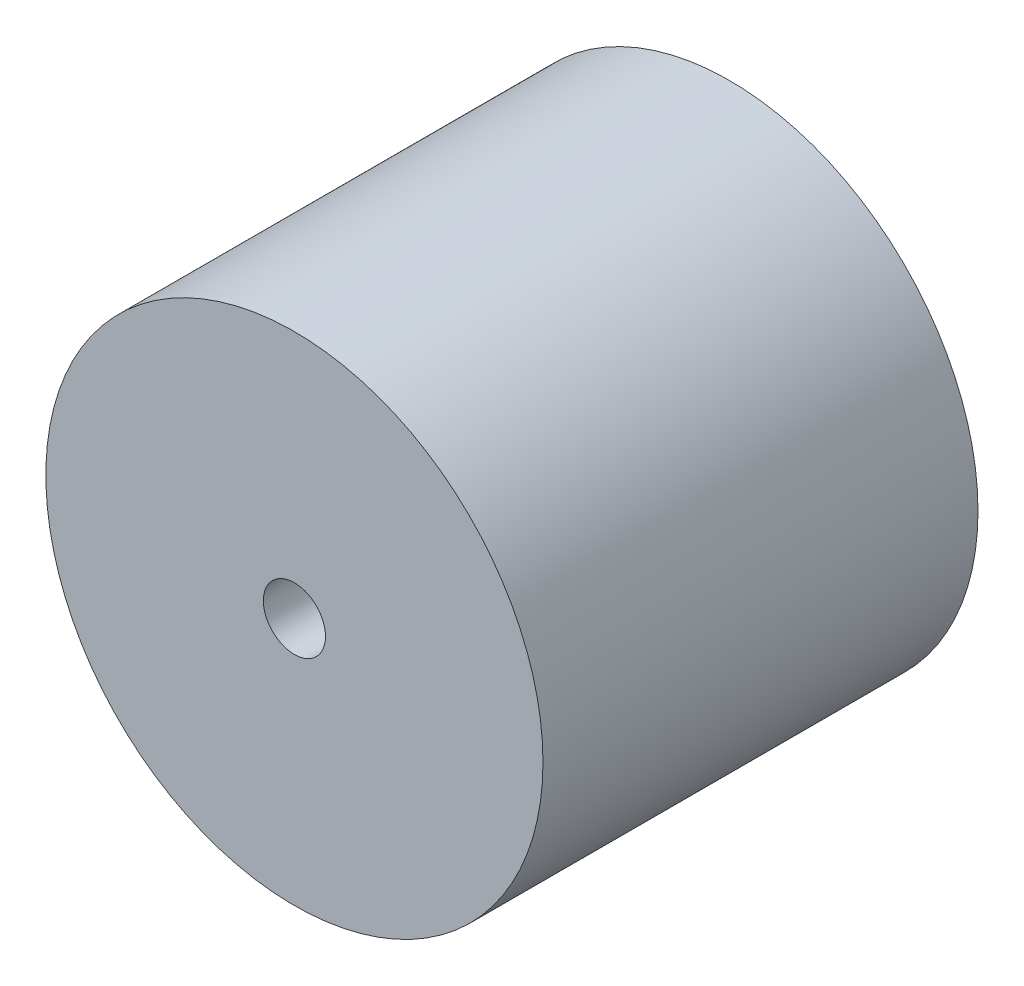
SolidWorks part; units mm, degrees
ref_plane "Front Plane" through (0, 0, 0) normal (0, 0, 1) x (1, 0, 0)
ref_plane "Top Plane" through (0, 0, 0) normal (0, 1, 0) x (1, 0, 0)
ref_plane "Right Plane" through (0, 0, 0) normal (1, 0, 0) x (0, 0, -1)
sketch "Sketch1" plane through (0, 0, 0) normal (0, 0, 1) x (1, 0, 0)
  circle A0 centre (0, 0) radius 20
  circle A1 centre (0, 0) radius 2.5
  dimension "D1" = 40
  dimension "D2" = 5
extrude "Boss-Extrude1" add sketch "Sketch1" along normal blind 35
